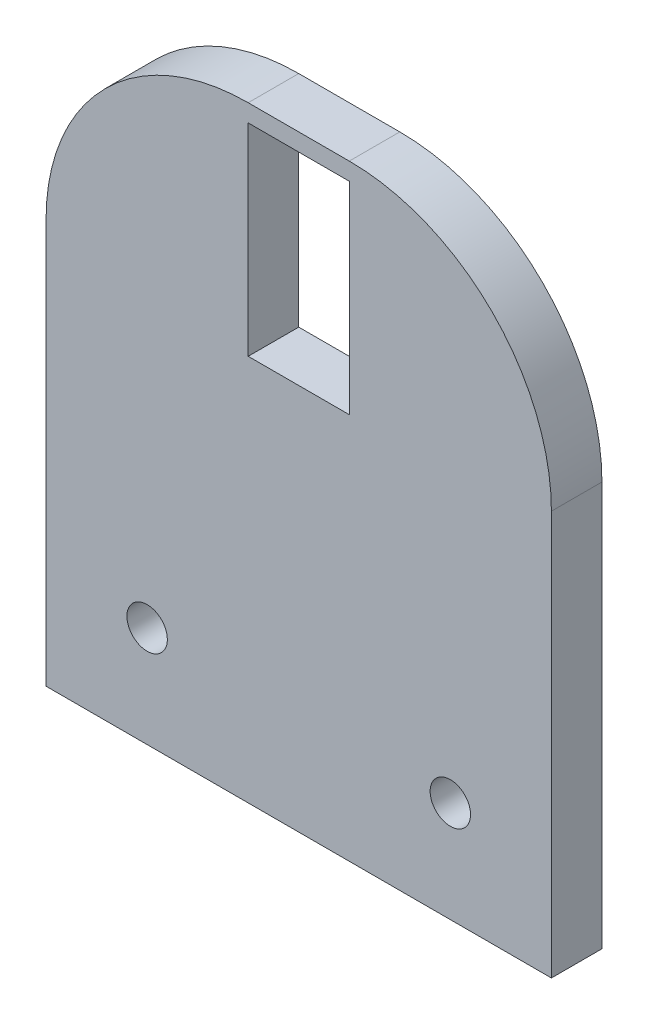
SolidWorks part; units mm, degrees
ref_plane "Front Plane" through (0, 0, 0) normal (0, 0, 1) x (1, 0, 0)
ref_plane "Top Plane" through (0, 0, 0) normal (0, 1, 0) x (1, 0, 0)
ref_plane "Right Plane" through (0, 0, 0) normal (1, 0, 0) x (0, 0, -1)
sketch "Sketch1" plane through (0, 0, 0) normal (0, 1, 0) x (1, 0, 0)
  line L1 (25, 2.5) -> (-25, 2.5)
  line L2 (25, 2.5) -> (25, -2.5)
  line L3 (25, -2.5) -> (-25, -2.5)
  line L4 (-25, 2.5) -> (-25, -2.5)
  line L5 (25, 2.5) -> (-25, -2.5) construction
  line L6 (25, -2.5) -> (-25, 2.5) construction
  point P0 (0, 0)
  dimension "D1" = 5
  dimension "D2" = 50
extrude "Boss-Extrude1" add sketch "Sketch1" along normal blind 60
fillet "Fillet1" radius 20 2 edges at (-25, 60, 0) (25, 60, 0)
sketch "Sketch2" plane through (0, 0, 2.5) normal (0, 0, 1) x (1, 0, 0)
  line L0 (-25, 40) -> (-25, 0) construction
  line L1 (-25, 0) -> (25, 0) construction
  line L2 (25, 40) -> (25, 0) construction
  line L4 (-5, 58.2714) -> (5, 58.2714)
  line L5 (-5, 58.2714) -> (-5, 38.2714)
  line L6 (-5, 38.2714) -> (5, 38.2714)
  line L7 (5, 58.2714) -> (5, 38.2714)
  line L8 (-5, 58.2714) -> (5, 38.2714) construction
  line L9 (-5, 38.2714) -> (5, 58.2714) construction
  circle A0 centre (-15, 10) radius 2
  circle A1 centre (15, 10) radius 2
  point P10 (0, 48.2714)
  dimension "D5" = 4
  dimension "D6" = 4
  dimension "D1" = 10
  dimension "D2" = 10
  dimension "D3" = 10
  dimension "D4" = 10
  dimension "D7" = 20
  dimension "D8" = 10
extrude "Cut-Extrude1" cut sketch "Sketch2" against normal blind 5
